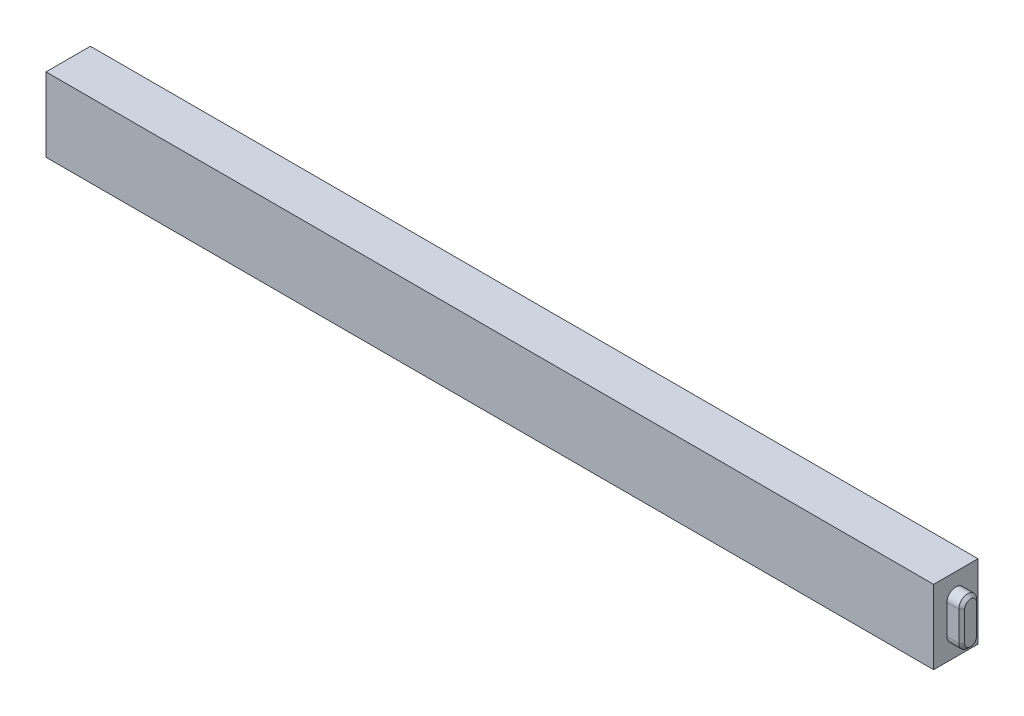
SolidWorks part; units mm, degrees
ref_plane "Plan de face" through (0, 0, 0) normal (0, 0, 1) x (1, 0, 0)
ref_plane "Plan de dessus" through (0, 0, 0) normal (0, 1, 0) x (1, 0, 0)
ref_plane "Plan de droite" through (0, 0, 0) normal (1, 0, 0) x (0, 0, -1)
sketch "Esquisse1" plane through (0, 0, 0) normal (0, 0, 1) x (1, 0, 0)
  line L1 (-300, 25) -> (300, 25)
  line L2 (-300, 25) -> (-300, -25)
  line L3 (-300, -25) -> (300, -25)
  line L4 (300, 25) -> (300, -25)
  line L5 (-300, 25) -> (300, -25) construction
  line L6 (-300, -25) -> (300, 25) construction
  point P0 (0, 0)
  dimension "D1" = 600
  dimension "D2" = 50
extrude "Boss.-Extru.1" add sketch "Esquisse1" along normal blind 30
sketch "Esquisse2" plane through (300, 0, 0) normal (1, 0, 0) x (0, 0, -1)
  line L0 (-15, 10) -> (-15, -10) construction
  line L1 (-9, 10) -> (-9, -10)
  line L2 (-21, 10) -> (-21, -10)
  line L3 (0, -25) -> (0, 25) construction
  line L4 (-30, 25) -> (0, 25) construction
  arc A0 (-9, 10) -> (-21, 10) centre (-15, 10) ccw
  arc A1 (-21, -10) -> (-9, -10) centre (-15, -10) ccw
  point P2 (-15, 0)
  dimension "D1" = 6
  dimension "D2" = 15
  dimension "D3" = 20
  dimension "D4" = 25
extrude "Boss.-Extru.2" add sketch "Esquisse2" along normal blind 10
chamfer "Chanfrein1" distance 2 angle 45 4 edges at (310, 0, 9) (310, -16, 15) (310, 0, 21) (310, 16, 15)
sketch "Esquisse3" plane through (-300, 0, 0) normal (-1, 0, 0) x (0, 0, 1)
  line L0 (15, 10) -> (15, -10) construction
  line L1 (21, 10) -> (21, -10)
  line L2 (9, 10) -> (9, -10)
  line L4 (30, 25) -> (0, 25) construction
  line L5 (30, 25) -> (30, -25) construction
  arc A0 (21, 10) -> (9, 10) centre (15, 10) ccw
  arc A1 (9, -10) -> (21, -10) centre (15, -10) ccw
  point P2 (15, 0)
  dimension "D3" = 6
  dimension "D1" = 25
  dimension "D2" = 20
  dimension "D4" = 15
extrude "Boss.-Extru.3" add sketch "Esquisse3" along normal blind 10 contours L2 A1 L1 A0
chamfer "Chanfrein2" distance 2 angle 45 4 edges at (-310, 0, 21) (-310, -16, 15) (-310, 0, 9) (-310, 16, 15)
